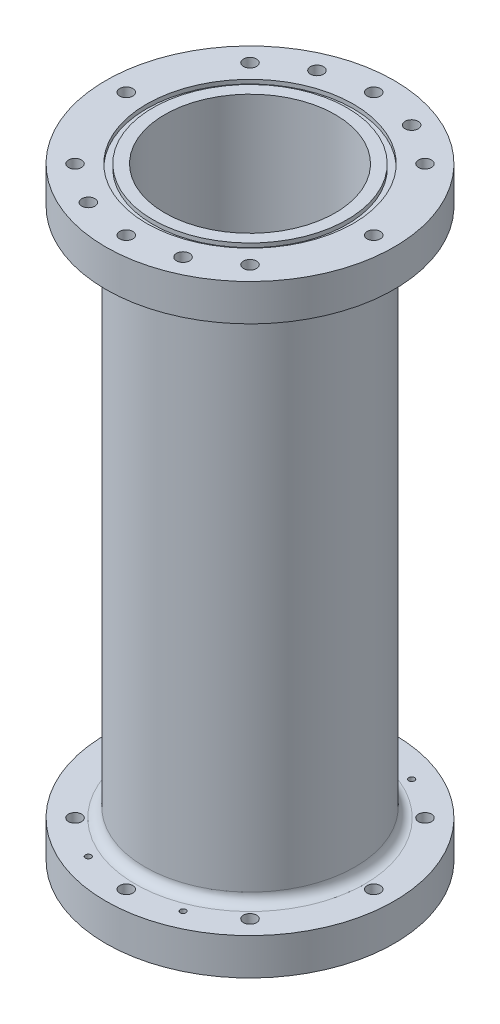
SolidWorks part; units mm, degrees
ref_plane "Front Plane" through (0, 0, 0) normal (0, 0, 1) x (1, 0, 0)
ref_plane "Top Plane" through (0, 0, 0) normal (0, 1, 0) x (1, 0, 0)
ref_plane "Right Plane" through (0, 0, 0) normal (1, 0, 0) x (0, 0, -1)
sketch "Sketch2" plane through (0, 0, 0) normal (0, 1, 0) x (1, 0, 0)
  circle A0 centre (0, 0) radius 41.275
  circle A1 centre (0, 0) radius 50.8
  dimension "D1" = 101.6
  dimension "D2" = 82.55
extrude "Base Cylinder" add sketch "Sketch2" along normal blind 292.1
sketch "Sketch3" plane through (0, 0, 0) normal (0, -1, 0) x (1, 0, 0)
  circle A0 centre (0, 0) radius 41.275
  circle A1 centre (0, 0) radius 69.85
  dimension "D1" = 139.7
extrude "Aft Flange" add sketch "Sketch3" against normal blind 17.78
sketch "Sketch4" plane through (0, 292.1, 0) normal (0, 1, 0) x (1, 0, 0)
  circle A0 centre (0, 0) radius 41.275
  circle A1 centre (0, 0) radius 69.85
extrude "Forward Flange" add sketch "Sketch4" against normal blind 17.78
sketch "Sketch6" plane through (0, 0, 0) normal (0, -1, 0) x (1, 0, 0)
  circle A0 centre (0, 0) radius 50.0761
  circle A1 centre (0, 0) radius 47.0027
  dimension "D1" = 100.1522
  dimension "D2" = 94.0054
extrude "O-Ring Slot 1" cut sketch "Sketch6" against normal blind 1.9812
sketch "Sketch7" plane through (0, 292.1, 0) normal (0, 1, 0) x (1, 0, 0)
  circle A0 centre (0, 0) radius 50.0761
  circle A1 centre (0, 0) radius 47.0027
  dimension "D1" = 100.1522
  dimension "D2" = 94.0054
extrude "O-Ring Slot 2" cut sketch "Sketch7" against normal blind 1.9812
sketch "Sketch8" plane through (0, 0, 0) normal (0, -1, 0) x (1, 0, 0)
  circle A0 centre (-59.9186, 0) radius 3.175
  circle A1 centre (-42.3688, 42.3688) radius 3.175
  circle A2 centre (0, 59.9186) radius 3.175
  circle A3 centre (42.3688, 42.3688) radius 3.175
  circle A4 centre (59.9186, 0) radius 3.175
  circle A5 centre (42.3688, -42.3688) radius 3.175
  circle A6 centre (0, -59.9186) radius 3.175
  circle A7 centre (-42.3688, -42.3688) radius 3.175
  point P36 (0, 0)
  dimension "D2" = 6.35
  dimension "D1" = 59.9186
  dimension "D3" = 8
extrude "Cut-Extrude4" cut sketch "Sketch8" against normal through all both and the other way through all
fillet "Fillet1" radius 4.7625 2 edges at (0, 17.78, -50.8) (0, 274.32, 50.8)
sketch "Sketch9" plane through (0, 292.1, 0) normal (0, 1, 0) x (1, 0, 0)
  line L0 (0, -76.2) -> (0, 76.2) construction
  line L1 (-32.6024, 78.7092) -> (32.6024, -78.7092) construction
  line L2 (-32.0538, -77.3847) -> (32.0538, 77.3847) construction
  circle A0 centre (0, 0) radius 59.9186 construction
  circle A1 centre (-22.9299, 55.3576) radius 3.175
  circle A2 centre (22.9299, -55.3576) radius 3.175
  circle A3 centre (22.9299, 55.3576) radius 3.175
  circle A4 centre (-22.9299, -55.3576) radius 3.175
  point P6 (0, 0)
  point P9 (0, 0)
  point P16 (0, 0)
  dimension "D1" = 119.8372
  dimension "D3" = 6.35
  dimension "D4" = 6.35
  dimension "D5" = 6.35
  dimension "D6" = 6.35
  dimension "D2" = 22.5
  dimension "D7" = 22.5
extrude "Cut-Extrude5" cut sketch "Sketch9" against normal blind 7.62
sketch "Sketch10" plane through (0, 0, 0) normal (0, -1, 0) x (1, 0, 0)
  line L0 (0, -76.2) -> (0, 76.2) construction
  line L1 (-33.7592, 81.5019) -> (33.7592, -81.5019) construction
  line L2 (-33.8465, -81.7128) -> (33.8465, 81.7128) construction
  circle A0 centre (0, 0) radius 59.9186 construction
  circle A1 centre (-22.9299, 55.3576) radius 3.175
  circle A2 centre (22.9299, -55.3576) radius 3.175
  circle A3 centre (22.9299, 55.3576) radius 3.175
  circle A4 centre (-22.9299, -55.3576) radius 3.175
  point P6 (0, 0)
  point P9 (0, 0)
  point P16 (0, 0)
  dimension "D1" = 119.8372
  dimension "D2" = 6.35
  dimension "D3" = 6.35
  dimension "D5" = 6.35
  dimension "D6" = 6.35
  dimension "D4" = 22.5
  dimension "D7" = 22.5
extrude "Cut-Extrude6" cut sketch "Sketch10" against normal blind 7.62
sketch "Sketch11" plane through (0, 284.48, 0) normal (0, 1, 0) x (1, 0, 0)
  circle A0 centre (-22.9299, 55.3576) radius 1.4097
  circle A1 centre (22.9299, 55.3576) radius 1.4097
  circle A2 centre (-22.9299, -55.3576) radius 1.4097
  circle A3 centre (22.9299, -55.3576) radius 1.4097
  dimension "D1" = 2.8194
  dimension "D2" = 2.8194
  dimension "D3" = 2.8194
  dimension "D4" = 2.8194
extrude "Cut-Extrude7" cut sketch "Sketch11" against normal up to next
sketch "Sketch12" plane through (0, 7.62, 0) normal (0, -1, 0) x (1, 0, 0)
  circle A0 centre (-22.9299, 55.3576) radius 1.4097
  circle A1 centre (22.9299, 55.3576) radius 1.4097
  circle A2 centre (-22.9299, -55.3576) radius 1.4097
  circle A3 centre (22.9299, -55.3576) radius 1.4097
  dimension "D1" = 2.8194
  dimension "D2" = 2.8194
  dimension "D3" = 2.8194
  dimension "D4" = 2.8194
extrude "Cut-Extrude8" cut sketch "Sketch12" against normal up to next
